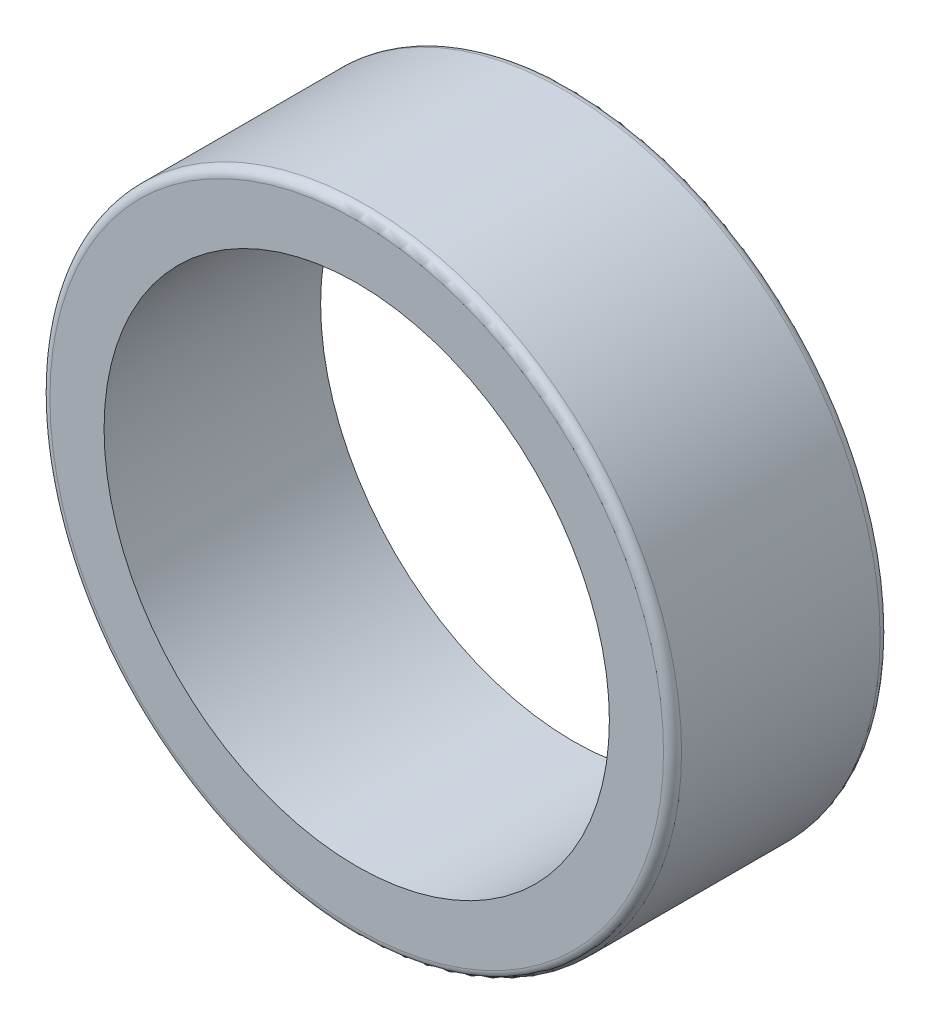
SolidWorks part; units mm, degrees
ref_plane "Front Plane" through (0, 0, 0) normal (0, 0, 1) x (1, 0, 0)
ref_plane "Top Plane" through (0, 0, 0) normal (0, 1, 0) x (1, 0, 0)
ref_plane "Right Plane" through (0, 0, 0) normal (1, 0, 0) x (0, 0, -1)
sketch "Esquisse1" plane through (0, 0, 0) normal (0, 0, 1) x (1, 0, 0)
  circle A0 centre (0, 0) radius 14
  circle A1 centre (0, 0) radius 17.5
  dimension "D1" = 35
  dimension "D2" = 28
extrude "Boss.-Extru.1" add sketch "Esquisse1" along normal blind 12
fillet "Congé1" radius 0.5 2 edges at (17.5, 0, 0) (17.5, 0, 12)
